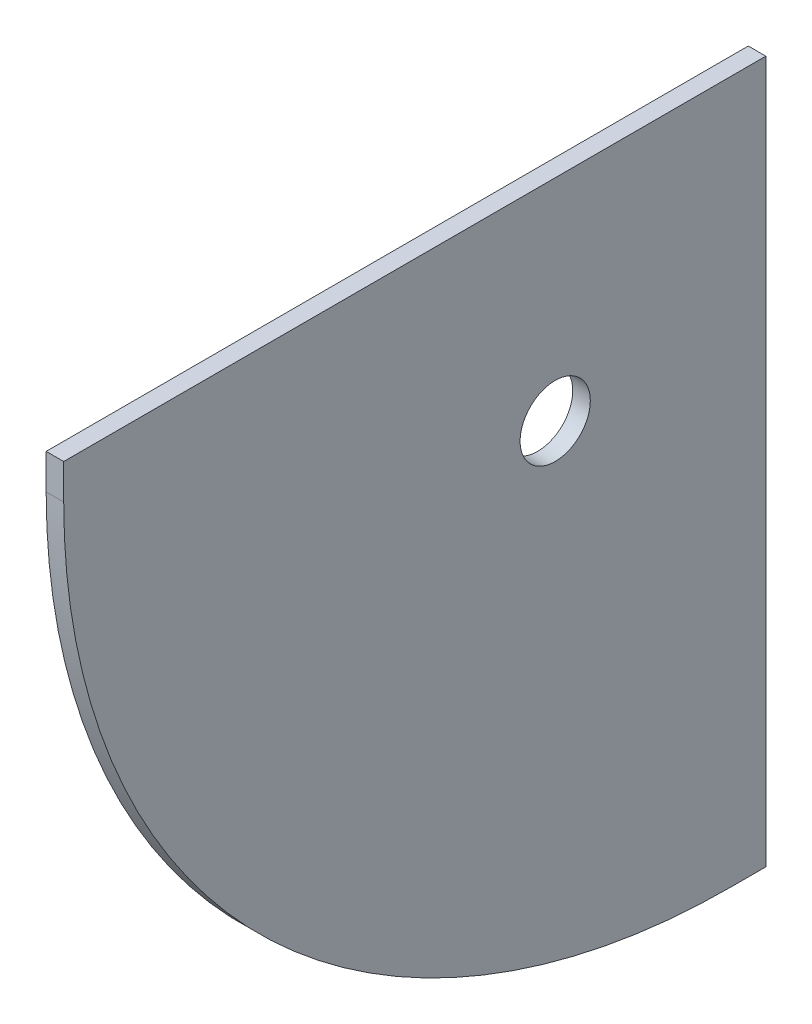
SolidWorks part; units mm, degrees
ref_plane "Front Plane" through (0, 0, 0) normal (0, 0, 1) x (1, 0, 0)
ref_plane "Top Plane" through (0, 0, 0) normal (0, 1, 0) x (1, 0, 0)
ref_plane "Right Plane" through (0, 0, 0) normal (1, 0, 0) x (0, 0, -1)
sketch "Sketch1" plane through (0, 0, 0) normal (1, 0, 0) x (0, 0, -1)
  line L1 (-127, 127) -> (127, 127)
  line L2 (-127, 127) -> (-127, -127)
  line L3 (-127, -127) -> (127, -127)
  line L4 (127, 127) -> (127, -127)
  line L5 (-127, 127) -> (127, -127) construction
  line L6 (-127, -127) -> (127, 127) construction
  point P0 (0, 0)
  dimension "D1" = 254
  dimension "D2" = 254
extrude "Boss-Extrude1" add sketch "Sketch1" along normal mid plane 6.35
fillet "Fillet1" radius 241.3 1 edges at (0, -127, 127)
sketch "Sketch2" plane through (3.175, 0, 0) normal (1, 0, 0) x (0, 0, -1)
  line L0 (127, -127) -> (127, 127) construction
  line L1 (127, 127) -> (-127, 127) construction
  circle A0 centre (50.8, 50.8) radius 12.7
  dimension "D1" = 25.4
  dimension "D2" = 76.2
  dimension "D3" = 76.2
extrude "Cut-Extrude1" cut sketch "Sketch2" against normal up to next
